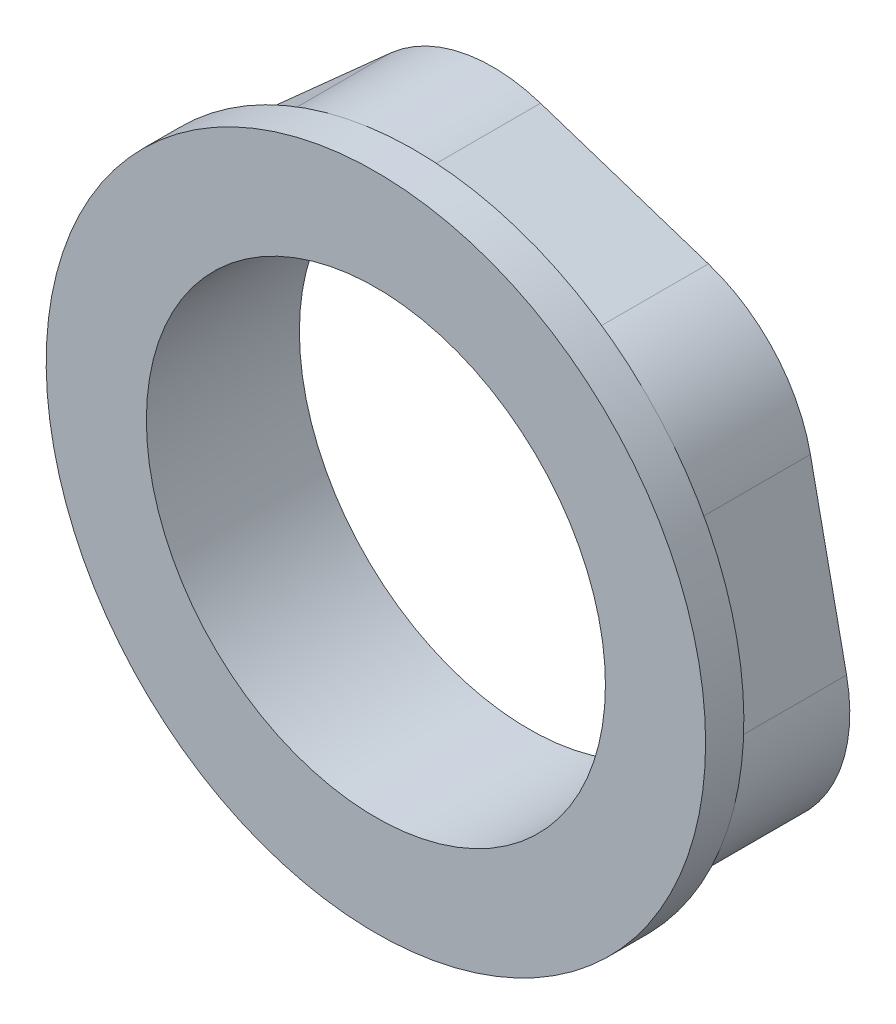
SolidWorks part; units mm, degrees
ref_plane "Front Plane" through (0, 0, 0) normal (0, 0, 1) x (1, 0, 0)
ref_plane "Top Plane" through (0, 0, 0) normal (0, 1, 0) x (1, 0, 0)
ref_plane "Right Plane" through (0, 0, 0) normal (1, 0, 0) x (0, 0, -1)
sketch "Sketch1" plane through (0, 0, 0) normal (0, 0, 1) x (1, 0, 0)
  line L1 (4.7265, -22.6052) -> (21.9399, -7.2093)
  line L2 (21.9399, -7.2093) -> (17.2134, 15.3959)
  line L3 (17.2134, 15.3959) -> (-4.7265, 22.6052)
  line L4 (-4.7265, 22.6052) -> (-21.9399, 7.2093)
  line L5 (-21.9399, 7.2093) -> (-17.2134, -15.3959)
  line L6 (-17.2134, -15.3959) -> (4.7265, -22.6052)
  circle A0 centre (0, 0) radius 15
  circle A1 centre (0, 0) radius 20 construction
  dimension "D1" = 30
  dimension "D2" = 40
extrude "Boss-Extrude1" add sketch "Sketch1" along normal blind 7.5
fillet "Fillet1" radius 10 6 edges at (-4.7265, 22.6052, 3.75) (-21.9399, 7.2093, 3.75) (-17.2134, -15.3959, 3.75) (4.7265, -22.6052, 3.75) (21.9399, -7.2093, 3.75) (17.2134, 15.3959, 3.75)
sketch "Sketch5" plane through (0, 0, 7.5) normal (0, 0, 1) x (1, 0, 0)
  circle A0 centre (0, 0) radius 15 construction
  circle A1 centre (0, 0) radius 15
  circle A2 centre (0, 0) radius 21.547
extrude "Boss-Extrude2" add sketch "Sketch5" along normal blind 2.5
